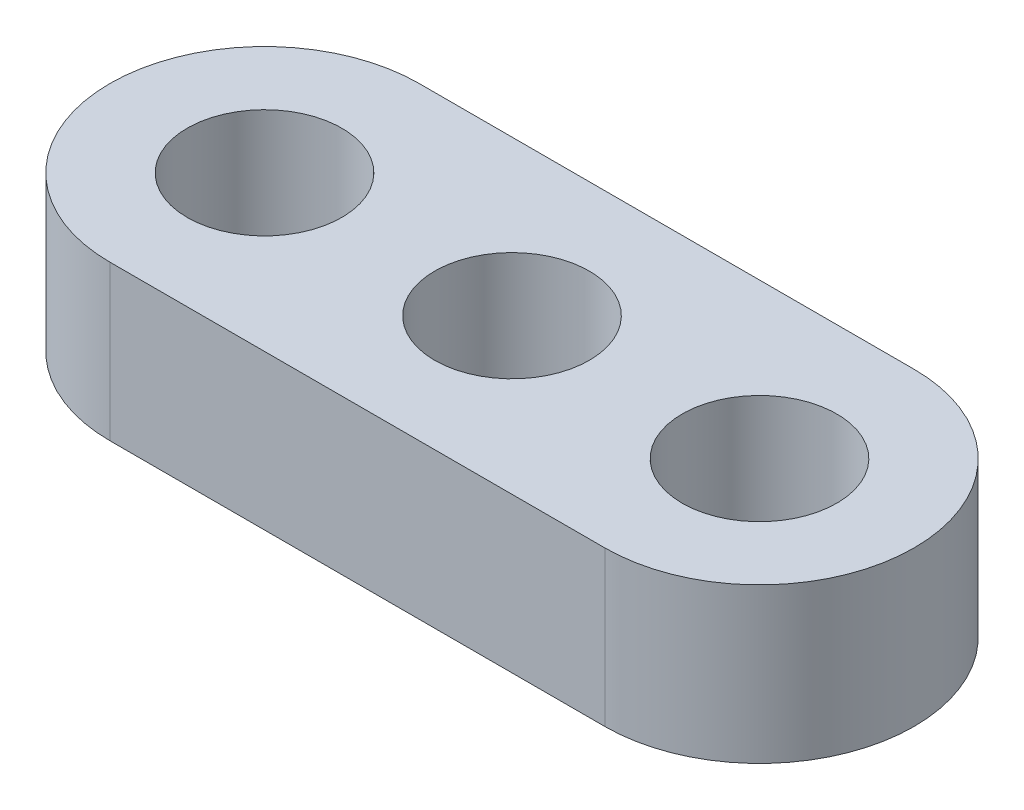
SolidWorks part; units mm, degrees
ref_plane "Front Plane" through (0, 0, 0) normal (0, 0, 1) x (1, 0, 0)
ref_plane "Top Plane" through (0, 0, 0) normal (0, 1, 0) x (1, 0, 0)
ref_plane "Right Plane" through (0, 0, 0) normal (1, 0, 0) x (0, 0, -1)
sketch "Sketch1" plane through (0, 0, 0) normal (0, 1, 0) x (1, 0, 0)
  line L0 (10.16, 3.175) -> (0, 3.175)
  line L1 (0, -3.175) -> (10.16, -3.175)
  circle A0 centre (0, 0) radius 1.5875
  circle A1 centre (5.08, 0) radius 1.5875
  circle A2 centre (10.16, 0) radius 1.5875
  arc A3 (10.16, -3.175) -> (10.16, 3.175) centre (10.16, 0) ccw
  arc A4 (0, 3.175) -> (0, -3.175) centre (0, 0) ccw
  dimension "D1" = 3.175
  dimension "D3" = 6.35
  dimension "D4" = 5.08
  dimension "D2" = 3
extrude "Boss-Extrude1" add sketch "Sketch1" along normal blind 3.175
